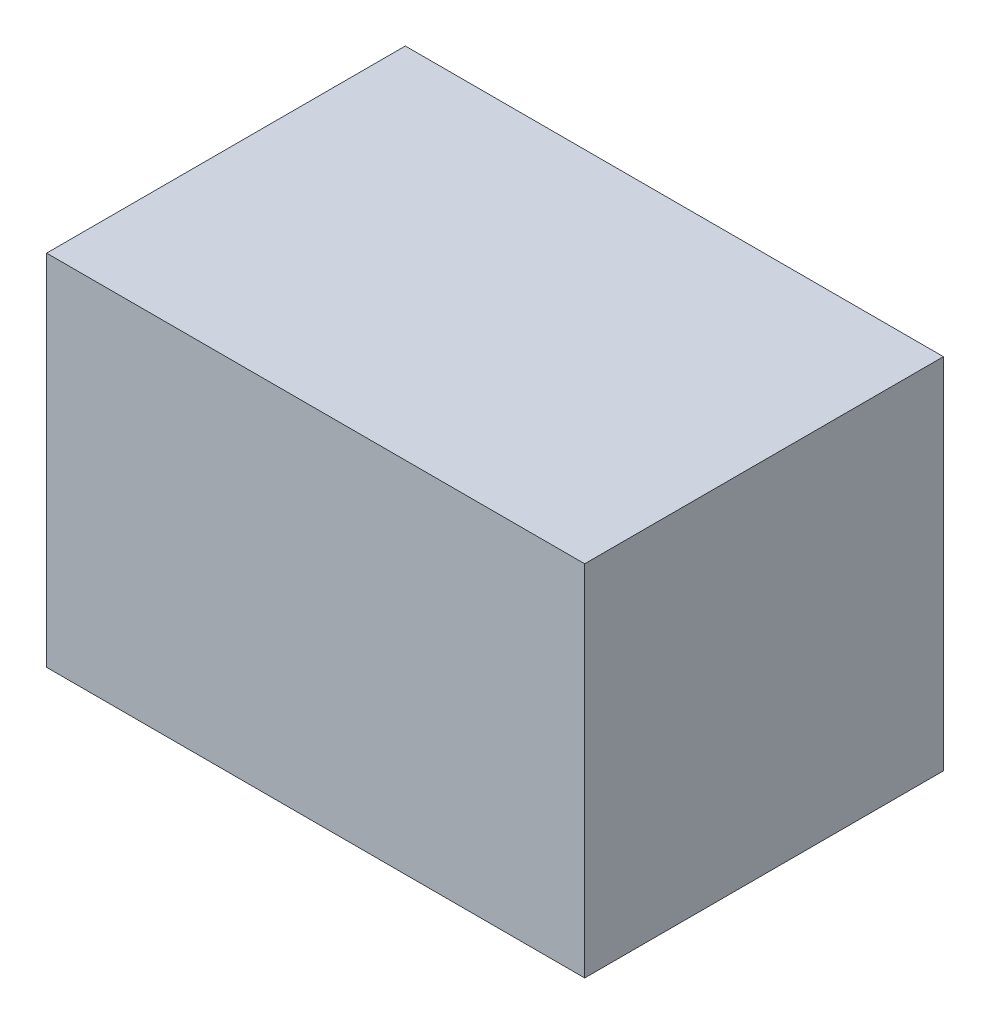
SolidWorks part; units mm, degrees
ref_plane "Front Plane" through (0, 0, 0) normal (0, 0, 1) x (1, 0, 0)
ref_plane "Top Plane" through (0, 0, 0) normal (0, 1, 0) x (1, 0, 0)
ref_plane "Right Plane" through (0, 0, 0) normal (1, 0, 0) x (0, 0, -1)
sketch "Sketch2" plane through (0, 0, 0) normal (0, 1, 0) x (1, 0, 0)
  line L1 (-228.6, -152.4) -> (228.6, -152.4)
  line L2 (-228.6, -152.4) -> (-228.6, 152.4)
  line L3 (-228.6, 152.4) -> (228.6, 152.4)
  line L4 (228.6, -152.4) -> (228.6, 152.4)
  line L5 (-228.6, -152.4) -> (228.6, 152.4) construction
  line L6 (-228.6, 152.4) -> (228.6, -152.4) construction
  point P0 (0, 0)
  dimension "D1" = 304.8
  dimension "D2" = 457.2
extrude "Boss-Extrude1" add sketch "Sketch2" along normal blind 304.8
